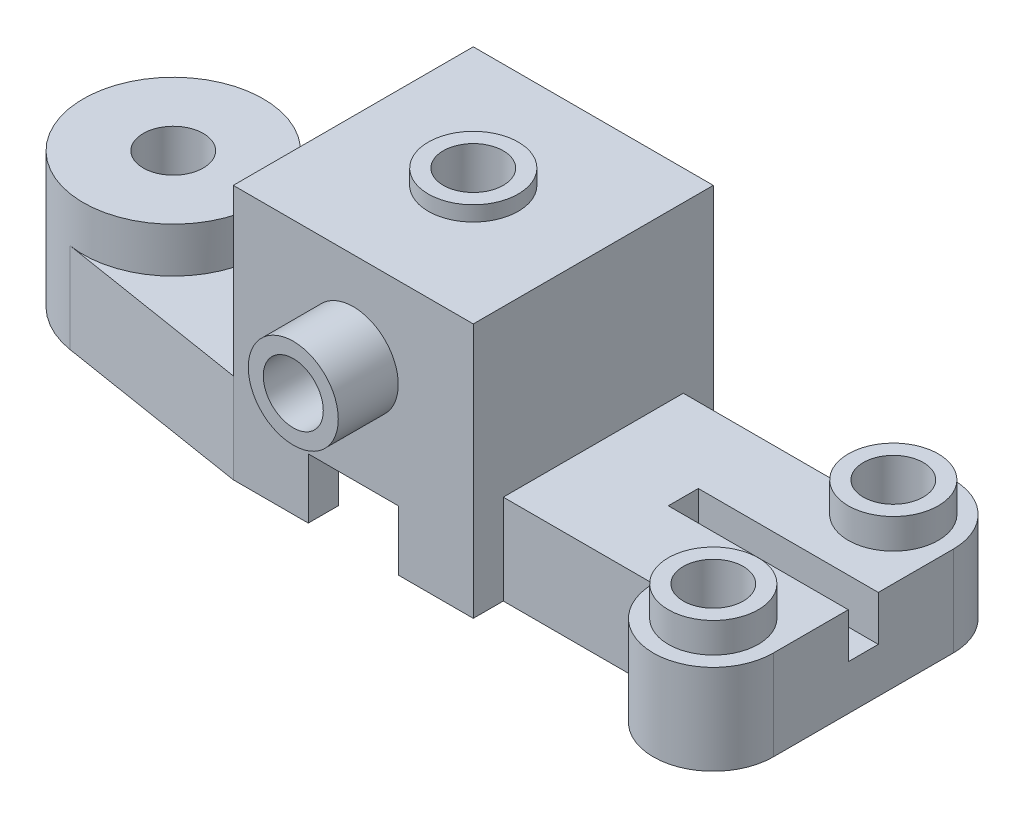
SolidWorks part; units mm, degrees
material "Plain Carbon Steel"
ref_plane "Front Plane" through (0, 0, 0) normal (0, 0, 1) x (1, 0, 0)
ref_plane "Top Plane" through (0, 0, 0) normal (0, 1, 0) x (1, 0, 0)
ref_plane "Right Plane" through (0, 0, 0) normal (1, 0, 0) x (0, 0, -1)
sketch "Sketch1" plane through (0, 0, 0) normal (0, 1, 0) x (1, 0, 0)
  line L0 (184.6318, 0) -> (-168.1602, 0) construction
  line L1 (130, 30) -> (130, -30)
  line L2 (90, 30) -> (40, 30)
  line L3 (40, 40) -> (40, 30)
  line L4 (40, 40) -> (-40, 40)
  line L6 (-40, -40) -> (40, -40)
  line L7 (-40, 40) -> (-104.7479, 29.6219)
  line L8 (-40, -40) -> (-104.7479, -29.6219)
  line L10 (40, -40) -> (40, -30)
  line L11 (90, -30) -> (40, -30)
  arc A1 (130, 30) -> (90, 30) centre (110, 30) ccw
  arc A2 (-104.7479, 29.6219) -> (-104.7479, -29.6219) centre (-100, 0) ccw
  arc A3 (130, -30) -> (90, -30) centre (110, -30) cw
  dimension "D2" = 20
  dimension "D9" = 60
  dimension "D1" = 60
  dimension "D3" = 110
  dimension "D4" = 70
  dimension "D5" = 80
  dimension "D6" = 80
  dimension "D8" = 100
extrude "Boss-Extrude2" add sketch "Sketch1" along normal blind 30
sketch "Sketch2" plane through (0, 30, 0) normal (0, 1, 0) x (1, 0, 0)
  line L1 (-40, -40) -> (40, -40)
  line L2 (-40, -40) -> (-40, 40)
  line L3 (-40, 40) -> (40, 40)
  line L4 (40, -40) -> (40, 40)
extrude "Boss-Extrude3" add sketch "Sketch2" along normal blind 55
sketch "Sketch3" plane through (0, 0, 0) normal (0, -1, 0) x (1, 0, 0)
  line L3 (-20, -30) -> (20, -30)
  line L4 (-30, -20) -> (-30, 20)
  line L5 (30, -20) -> (30, 20)
  line L6 (-20, 30) -> (20, 30)
  line L7 (-155.0816, 0) -> (155.0816, 0) construction
  line L8 (0, 55.939) -> (0, -55.939) construction
  arc A0 (30, 20) -> (20, 30) centre (20, 20) ccw
  arc A1 (-30, 20) -> (-20, 30) centre (-20, 20) cw
  arc A2 (-30, -20) -> (-20, -30) centre (-20, -20) ccw
  arc A3 (20, -30) -> (30, -20) centre (20, -20) ccw
  point P3 (0, 0)
  point P6 (0, 0)
  point P7 (0, 0)
  point P15 (30, 30)
  point P18 (-30, 30)
  point P21 (-30, -30)
  point P24 (30, -30)
  dimension "D2" = 10
  dimension "D1" = 60
extrude "Cut-Extrude1" cut sketch "Sketch3" against normal blind 70
sketch "Sketch4" plane through (0, 85, 0) normal (0, 1, 0) x (1, 0, 0)
  circle A0 centre (0, 0) radius 15
  dimension "D1" = 30
extrude "Boss-Extrude4" add sketch "Sketch4" along normal blind 5
sketch "Sketch6" plane through (0, 90, 0) normal (0, 1, 0) x (1, 0, 0)
  circle A0 centre (0, 0) radius 10
  dimension "D1" = 20
extrude "Cut-Extrude2" cut sketch "Sketch6" against normal through all
sketch "Sketch7" plane through (0, 30, 0) normal (0, 1, 0) x (1, 0, 0)
  circle A0 centre (-100, 0) radius 30
  arc A1 (-104.7479, 29.6219) -> (-104.7479, -29.6219) centre (-100, 0) ccw construction
extrude "Boss-Extrude5" add sketch "Sketch7" along normal blind 15
sketch "Sketch8" plane through (0, 45, 0) normal (0, 1, 0) x (1, 0, 0)
  circle A0 centre (-100, 0) radius 10
  dimension "D1" = 20
extrude "Cut-Extrude3" cut sketch "Sketch8" against normal through all
sketch "Sketch9" plane through (0, 0, 0) normal (0, -1, 0) x (1, 0, 0)
  line L0 (-50, 28.2695) -> (-50, -28.2695)
  line L1 (-50, -28.2695) -> (-103.1653, -19.7479)
  line L2 (-50, 28.2695) -> (-103.1653, 19.7479)
  line L3 (-216.7656, 0) -> (16.7656, 0) construction
  line L4 (-104.7479, 29.6219) -> (-40, 40) construction
  arc A0 (-103.1653, 19.7479) -> (-103.1653, -19.7479) centre (-100, 0) ccw
  point P10 (-100, 0)
  dimension "D1" = 20
  dimension "D2" = 50
extrude "Cut-Extrude4" cut sketch "Sketch9" against normal blind 15
sketch "Sketch11" plane through (0, 0, 40) normal (0, 0, 1) x (1, 0, 0)
  line L0 (0, 26.0925) -> (0, -26.0925) construction
  line L1 (-15, 20) -> (15, 20)
  line L2 (15, 20) -> (15, 0)
  line L3 (-40, 0) -> (40, 0) construction
  line L4 (-15, 20) -> (-15, 0)
  line L6 (-15, 0) -> (15, 0)
  point P4 (0, 0)
  point P13 (0, 20)
  dimension "D1" = 30
  dimension "D2" = 20
extrude "Cut-Extrude5" cut sketch "Sketch11" against normal through all
sketch "Sketch12" plane through (0, 0, 40) normal (0, 0, 1) x (1, 0, 0)
  line L0 (0, 0) -> (0, 105.7752) construction
  circle A0 centre (0, 55) radius 15
  dimension "D1" = 30
  dimension "D2" = 55
extrude "Boss-Extrude6" add sketch "Sketch12" along normal blind 20
sketch "Sketch13" plane through (0, 0, 60) normal (0, 0, 1) x (1, 0, 0)
  circle A0 centre (0, 55) radius 10
  dimension "D1" = 20
extrude "Cut-Extrude6" cut sketch "Sketch13" against normal up to next
sketch "Sketch14" plane through (0, 30, 0) normal (0, 1, 0) x (1, 0, 0)
  circle A0 centre (110, -30) radius 15
  circle A1 centre (110, 30) radius 15
  dimension "D1" = 30
extrude "Boss-Extrude7" add sketch "Sketch14" along normal blind 10
sketch "Sketch15" plane through (0, 40, 0) normal (0, 1, 0) x (1, 0, 0)
  circle A0 centre (110, -30) radius 10
  circle A1 centre (110, 30) radius 10
  dimension "D1" = 20
extrude "Cut-Extrude7" cut sketch "Sketch15" against normal blind 15
sketch "Sketch16" plane through (0, 25, 0) normal (0, 1, 0) x (1, 0, 0)
  circle A0 centre (110, -30) radius 5
  circle A1 centre (110, 30) radius 5
  dimension "D1" = 10
extrude "Cut-Extrude8" cut sketch "Sketch16" against normal through all
sketch "Sketch17" plane through (0, 30, 0) normal (0, 1, 0) x (1, 0, 0)
  line L0 (161.582, 0) -> (-161.582, 0) construction
  line L1 (130, -30) -> (130, 30) construction
  line L2 (70, -5) -> (130, -5)
  line L3 (70, -5) -> (70, 5)
  line L4 (70, 5) -> (130, 5)
  line L5 (130, -5) -> (130, 5)
  point P6 (0, 0)
  dimension "D1" = 10
  dimension "D2" = 60
extrude "Cut-Extrude9" cut sketch "Sketch17" against normal blind 15
sketch "Sketch18" plane through (0, 0, 0) normal (0, 0, 1) x (1, 0, 0)
  line L0 (-70, 45) -> (-40, 85)
rib "Rib1" sketch "Sketch18" sketch "Sketch18" thickness 10 extrusion direction parallel to sketch draft on no parameters "D1"=10
